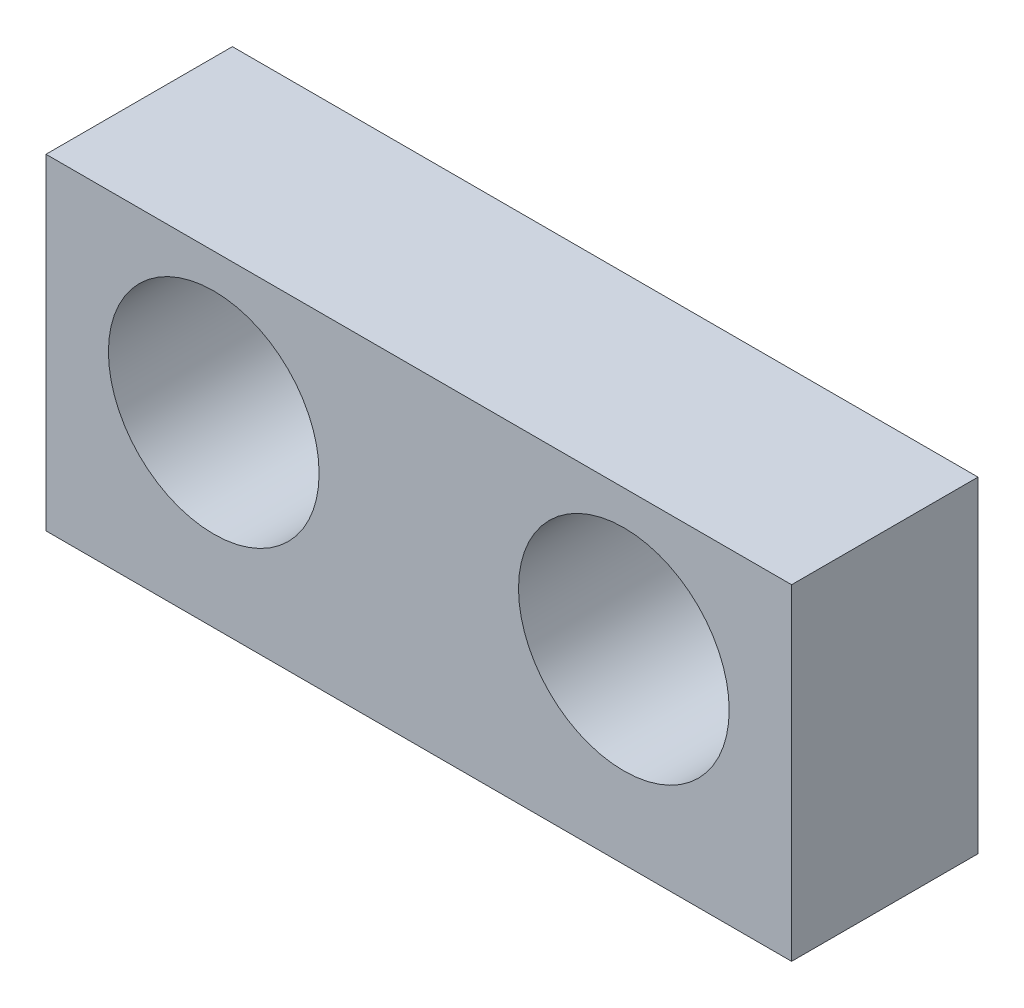
SolidWorks part; units mm, degrees
material "6061-T6 (SS)"
ref_plane "Front" through (0, 0, 0) normal (0, 0, 1) x (1, 0, 0)
ref_plane "Top" through (0, 0, 0) normal (0, 1, 0) x (1, 0, 0)
ref_plane "Right" through (0, 0, 0) normal (1, 0, 0) x (0, 0, -1)
sketch "Sketch1" plane through (0, 0, 0) normal (0, 0, 1) x (1, 0, 0)
  line L1 (-4, 3) -> (4, 3)
  line L2 (-4, 3) -> (-4, -0.5)
  line L3 (-4, -0.5) -> (4, -0.5)
  line L4 (4, 3) -> (4, -0.5)
  dimension "D1" = 4
  dimension "D2" = 4
  dimension "D3" = 3
  dimension "D4" = 0.5
extrude "Extrude1" add sketch "Sketch1" against normal blind 2
sketch "Sketch2" plane through (0, 0, 0) normal (0, 0, 1) x (1, 0, 0)
  line L0 (4, 3) -> (-4, 3) construction
  circle A0 centre (-2.2, 1.5) radius 1.1303
  circle A1 centre (2.2, 1.5) radius 1.1303
  dimension "D4" = 2.2606
  dimension "D5" = 2.2606
  dimension "D1" = 1.5
  dimension "D2" = 2.2
  dimension "D3" = 2.2
extrude "Extrude2" cut sketch "Sketch2" against normal through all
